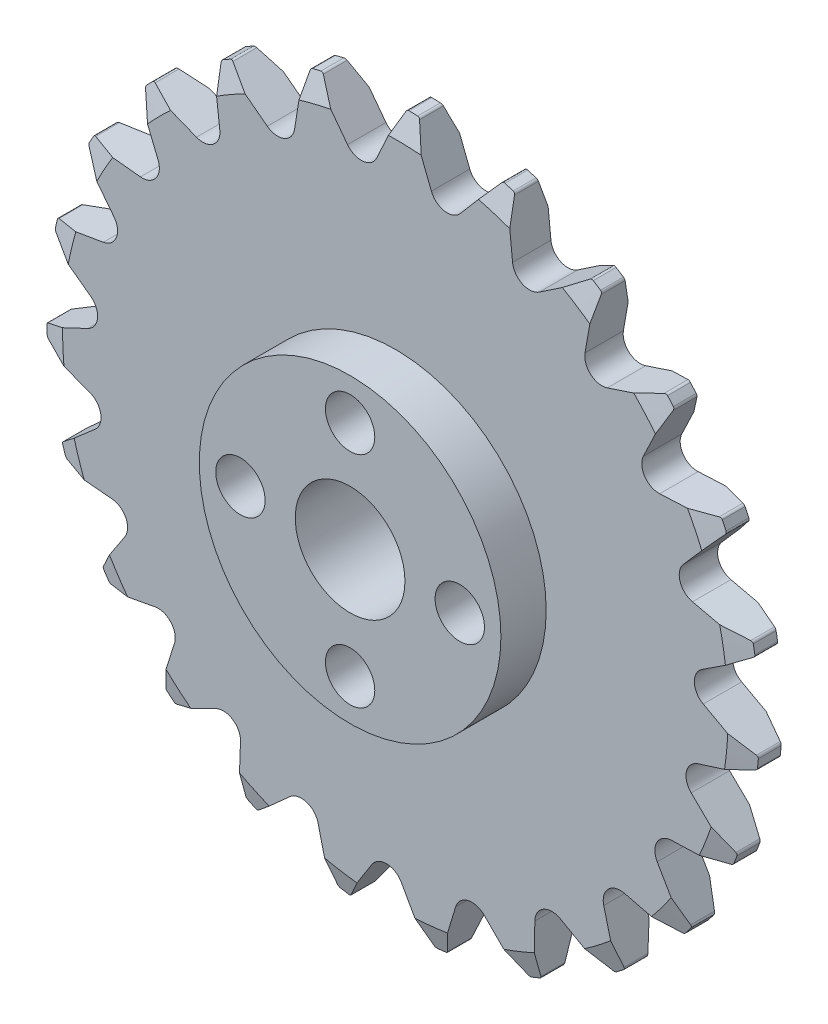
SolidWorks part; units mm, degrees
material "2024 Alloy"
ref_plane "Front Plane" through (0, 0, 0) normal (0, 0, 1) x (1, 0, 0)
ref_plane "Top Plane" through (0, 0, 0) normal (0, 1, 0) x (1, 0, 0)
ref_plane "Right Plane" through (0, 0, 0) normal (1, 0, 0) x (0, 0, -1)
sketch "Sketch1" plane through (0, 0, 0) normal (0, 1, 0) x (1, 0, 0)
  line L0 (26, 2.8) -> (0, 2.8)
  line L1 (0, 2.8) -> (0, 0)
  line L2 (0, 0) -> (26, 0)
  line L3 (26, 0) -> (26, 2.8)
  line L4 (0, 2.8) -> (0, 0) construction
revolve "Revolve1" add sketch "Sketch1" angle 360 about L4
sketch "Sketch2" plane through (0, 0, -2.8) normal (0, 0, -1) x (-1, 0, 0)
  line L0 (18.8013, 17.9586) -> (17.3085, 14.3114)
  line L1 (18.595, 12.5946) -> (22.5146, 13.0035)
  arc A0 (22.5146, 13.0035) -> (18.8013, 17.9586) centre (0, 0) ccw
  arc A1 (17.3085, 14.3114) -> (18.595, 12.5946) centre (18.4653, 13.8379) ccw
extrude "Cut-Extrude1" cut sketch "Sketch2" against normal through all
sketch "Sketch3" plane through (0, 0, -2.8) normal (0, 0, -1) x (-1, 0, 0)
  line L0 (22.9493, 12.2201) -> (20.5278, 9.1109)
  line L1 (21.3035, 7.1107) -> (25.188, 6.4469)
  arc A0 (25.188, 6.4469) -> (22.9493, 12.2201) centre (0, 0) ccw
  arc A1 (20.5278, 9.1109) -> (21.3035, 7.1107) centre (21.514, 8.3429) ccw
extrude "Cut-Extrude2" cut sketch "Sketch3" against normal through all
sketch "Sketch4" plane through (0, 0, -2.8) normal (0, 0, -1) x (-1, 0, 0)
  line L0 (25.3952, 5.5753) -> (22.2247, 3.2347)
  line L1 (22.4319, 1.0994) -> (25.9934, -0.5878)
  arc A0 (25.9934, -0.5878) -> (25.3952, 5.5753) centre (0, 0) ccw
  arc A1 (22.2247, 3.2347) -> (22.4319, 1.0994) centre (22.9671, 2.2291) ccw
extrude "Cut-Extrude3" cut sketch "Sketch4" against normal through all
sketch "Sketch5" plane through (0, 0, -2.8) normal (0, 0, -1) x (-1, 0, 0)
  line L0 (25.9577, -1.483) -> (22.2732, -2.8814)
  line L1 (21.8967, -4.9934) -> (24.8709, -7.5789)
  arc A0 (24.8709, -7.5789) -> (25.9577, -1.483) centre (0, 0) ccw
  arc A1 (22.2732, -2.8814) -> (21.8967, -4.9934) centre (22.7168, -4.05) ccw
extrude "Cut-Extrude4" cut sketch "Sketch5" against normal through all
sketch "Sketch6" plane through (0, 0, -2.8) normal (0, 0, -1) x (-1, 0, 0)
  line L0 (24.595, -8.4313) -> (20.6699, -8.7838)
  line L1 (19.7375, -10.7159) -> (21.9038, -14.0079)
  arc A0 (21.9038, -14.0079) -> (24.595, -8.4313) centre (0, 0) ccw
  arc A1 (20.6699, -8.7838) -> (19.7375, -10.7159) centre (20.7817, -10.0288) ccw
extrude "Cut-Extrude5" cut sketch "Sketch6" against normal through all
sketch "Sketch7" plane through (0, 0, -2.8) normal (0, 0, -1) x (-1, 0, 0)
  line L0 (21.4082, -14.7543) -> (17.5336, -14.0347)
  line L1 (16.1145, -15.6436) -> (17.3123, -19.3981)
  arc A0 (17.3123, -19.3981) -> (21.4082, -14.7543) centre (0, 0) ccw
  arc A1 (17.5336, -14.0347) -> (16.1145, -15.6436) centre (17.3053, -15.2637) ccw
extrude "Cut-Extrude6" cut sketch "Sketch7" against normal through all
sketch "Sketch8" plane through (0, 0, -2.8) normal (0, 0, -1) x (-1, 0, 0)
  line L0 (16.6337, -19.983) -> (13.0969, -18.2448)
  line L1 (11.2963, -19.4112) -> (11.4367, -23.3495)
  arc A0 (11.4367, -23.3495) -> (16.6337, -19.983) centre (0, 0) ccw
  arc A1 (13.0969, -18.2448) -> (11.2963, -19.4112) centre (12.5455, -19.3666) ccw
extrude "Cut-Extrude7" cut sketch "Sketch8" against normal through all
sketch "Sketch9" plane through (0, 0, -2.8) normal (0, 0, -1) x (-1, 0, 0)
  line L0 (10.6255, -23.7297) -> (7.6888, -21.1017)
  line L1 (5.6403, -21.7391) -> (4.713, -25.5693)
  arc A0 (4.713, -25.5693) -> (10.6255, -23.7297) centre (0, 0) ccw
  arc A1 (7.6888, -21.1017) -> (5.6403, -21.7391) centre (6.8552, -22.0332) ccw
extrude "Cut-Extrude8" cut sketch "Sketch9" against normal through all
sketch "Sketch10" plane through (0, 0, -2.8) normal (0, 0, -1) x (-1, 0, 0)
  line L0 (3.8293, -25.7165) -> (1.7105, -22.3936)
  line L1 (-0.4339, -22.4547) -> (-2.3603, -25.8926)
  arc A0 (-2.3603, -25.8926) -> (3.8293, -25.7165) centre (0, 0) ccw
  arc A1 (1.7105, -22.3936) -> (-0.4339, -22.4547) centre (0.6565, -23.0657) ccw
extrude "Cut-Extrude9" cut sketch "Sketch10" against normal through all
sketch "Sketch11" plane through (0, 0, -2.8) normal (0, 0, -1) x (-1, 0, 0)
  line L0 (-3.2509, -25.796) -> (-4.3946, -22.0247)
  line L1 (-6.476, -21.5049) -> (-9.2585, -24.2957)
  arc A0 (-9.2585, -24.2957) -> (-3.2509, -25.796) centre (0, 0) ccw
  arc A1 (-4.3946, -22.0247) -> (-6.476, -21.5049) centre (-5.5908, -22.3875) ccw
extrude "Cut-Extrude10" cut sketch "Sketch11" against normal through all
sketch "Sketch12" plane through (0, 0, -2.8) normal (0, 0, -1) x (-1, 0, 0)
  line L0 (-10.0901, -23.9623) -> (-10.1739, -20.0223)
  line L1 (-12.0379, -18.9602) -> (-15.4701, -20.8968)
  arc A0 (-15.4701, -20.8968) -> (-10.0901, -23.9623) centre (0, 0) ccw
  arc A1 (-10.1739, -20.0223) -> (-12.0379, -18.9602) centre (-11.4236, -20.0489) ccw
extrude "Cut-Extrude11" cut sketch "Sketch12" against normal through all
sketch "Sketch13" plane through (0, 0, -2.8) normal (0, 0, -1) x (-1, 0, 0)
  line L0 (-16.1808, -20.3514) -> (-15.1985, -16.5349)
  line L1 (-16.7069, -15.0093) -> (-20.5343, -15.9481)
  arc A0 (-20.5343, -15.9481) -> (-16.1808, -20.3514) centre (0, 0) ccw
  arc A1 (-15.1985, -16.5349) -> (-16.7069, -15.0093) centre (-16.4091, -16.2234) ccw
extrude "Cut-Extrude12" cut sketch "Sketch13" against normal through all
sketch "Sketch14" plane through (0, 0, -2.8) normal (0, 0, -1) x (-1, 0, 0)
  line L0 (-21.0716, -15.2312) -> (-19.096, -11.8213)
  line L1 (-20.1368, -9.9453) -> (-24.0756, -9.8167)
  arc A0 (-24.0756, -9.8167) -> (-21.0716, -15.2312) centre (0, 0) ccw
  arc A1 (-19.096, -11.8213) -> (-20.1368, -9.9453) centre (-20.1776, -11.1946) ccw
extrude "Cut-Extrude13" cut sketch "Sketch14" against normal through all
sketch "Sketch15" plane through (0, 0, -2.8) normal (0, 0, -1) x (-1, 0, 0)
  line L0 (-24.3995, -8.9813) -> (-21.5772, -6.2309)
  line L1 (-22.0733, -4.1437) -> (-25.8313, -2.9571)
  arc A0 (-25.8313, -2.9571) -> (-24.3995, -8.9813) centre (0, 0) ccw
  arc A1 (-21.5772, -6.2309) -> (-22.0733, -4.1437) centre (-22.4496, -5.3357) ccw
extrude "Cut-Extrude14" cut sketch "Sketch15" against normal through all
sketch "Sketch16" plane through (0, 0, -2.8) normal (0, 0, -1) x (-1, 0, 0)
  line L0 (-25.9178, -2.0654) -> (-22.4581, -0.1783)
  line L1 (-22.3727, 1.9653) -> (-25.6712, 4.1217)
  arc A0 (-25.6712, 4.1217) -> (-25.9178, -2.0654) centre (0, 0) ccw
  arc A1 (-22.4581, -0.1783) -> (-22.3727, 1.9653) centre (-23.0567, 0.919) ccw
extrude "Cut-Extrude15" cut sketch "Sketch16" against normal through all
sketch "Sketch17" plane through (0, 0, -2.8) normal (0, 0, -1) x (-1, 0, 0)
  line L0 (-25.514, 5.0037) -> (-21.6734, 5.8874)
  line L1 (-21.0128, 7.9285) -> (-23.6072, 10.8949)
  arc A0 (-23.6072, 10.8949) -> (-25.514, 5.0037) centre (0, 0) ccw
  arc A1 (-21.6734, 5.8874) -> (-21.0128, 7.9285) centre (-21.9537, 7.1056) ccw
extrude "Cut-Extrude16" cut sketch "Sketch17" against normal through all
sketch "Sketch18" plane through (0, 0, -2.8) normal (0, 0, -1) x (-1, 0, 0)
  line L0 (-23.2178, 11.7018) -> (-19.2813, 11.5165)
  line L1 (-18.0945, 13.3037) -> (-19.7924, 16.86)
  arc A0 (-19.7924, 16.86) -> (-23.2178, 11.7018) centre (0, 0) ccw
  arc A1 (-19.2813, 11.5165) -> (-18.0945, 13.3037) centre (-19.2226, 12.7651) ccw
extrude "Cut-Extrude17" cut sketch "Sketch18" against normal through all
sketch "Sketch19" plane through (0, 0, -2.8) normal (0, 0, -1) x (-1, 0, 0)
  line L0 (-19.1998, 17.5319) -> (-15.4592, 16.2915)
  line L1 (-13.8342, 17.6922) -> (-14.5097, 21.5748)
  arc A0 (-14.5097, 21.5748) -> (-19.1998, 17.5319) centre (0, 0) ccw
  arc A1 (-15.4592, 16.2915) -> (-13.8342, 17.6922) centre (-15.0657, 17.478) ccw
extrude "Cut-Extrude18" cut sketch "Sketch19" against normal through all
sketch "Sketch20" plane through (0, 0, -2.8) normal (0, 0, -1) x (-1, 0, 0)
  line L0 (-13.7577, 22.0618) -> (-10.4905, 19.8582)
  line L1 (-8.5479, 20.7685) -> (-8.1508, 24.6894)
  arc A0 (-8.1508, 24.6894) -> (-13.7577, 22.0618) centre (0, 0) ccw
  arc A1 (-10.4905, 19.8582) -> (-8.5479, 20.7685) centre (-9.7916, 20.8945) ccw
extrude "Cut-Extrude19" cut sketch "Sketch20" against normal through all
sketch "Sketch21" plane through (0, 0, -2.8) normal (0, 0, -1) x (-1, 0, 0)
  line L0 (-7.2953, 24.9555) -> (-4.7438, 21.9521)
  line L1 (-2.6277, 22.3046) -> (-1.1874, 25.9729)
  arc A0 (-1.1874, 25.9729) -> (-7.2953, 24.9555) centre (0, 0) ccw
  arc A1 (-4.7438, 21.9521) -> (-2.6277, 22.3046) centre (-3.7912, 22.7614) ccw
extrude "Cut-Extrude20" cut sketch "Sketch21" against normal through all
sketch "Sketch22" plane through (0, 0, -2.8) normal (0, 0, -1) x (-1, 0, 0)
  line L0 (-0.2919, 25.9984) -> (1.3547, 22.418)
  line L1 (3.4875, 22.1864) -> (5.864, 25.3301)
  arc A0 (5.864, 25.3301) -> (-0.2919, 25.9984) centre (0, 0) ccw
  arc A1 (1.3547, 22.418) -> (3.4875, 22.1864) centre (2.4903, 22.9402) ccw
extrude "Cut-Extrude21" cut sketch "Sketch22" against normal through all
sketch "Sketch23" plane through (0, 0, -2.8) normal (0, 0, -1) x (-1, 0, 0)
  line L0 (6.7332, 25.113) -> (7.3527, 21.2211)
  line L1 (9.344, 20.4228) -> (12.4805, 22.8087)
  arc A0 (12.4805, 22.8087) -> (6.7332, 25.113) centre (0, 0) ccw
  arc A1 (7.3527, 21.2211) -> (9.344, 20.4228) centre (8.5872, 21.4176) ccw
extrude "Cut-Extrude22" cut sketch "Sketch23" against normal through all
sketch "Sketch24" plane through (0, 0, -2.8) normal (0, 0, -1) x (-1, 0, 0)
  line L0 (13.2589, 22.3652) -> (12.8055, 18.4505)
  line L1 (14.5075, 17.1445) -> (18.1714, 18.5957)
  arc A0 (18.1714, 18.5957) -> (13.2589, 22.3652) centre (0, 0) ccw
  arc A1 (12.8055, 18.4505) -> (14.5075, 17.1445) centre (14.0472, 18.3066) ccw
extrude "Cut-Extrude23" cut sketch "Sketch24" against normal through all
sketch "Sketch25" plane through (0, 0, 0) normal (0, 1, 0) x (1, 0, 0)
  line L0 (11, 0) -> (0, 0)
  line L1 (0, 0) -> (0, -3.302)
  line L2 (0, -3.302) -> (11, -3.302)
  line L3 (11, -3.302) -> (11, 0)
  line L4 (0, 0) -> (0, -3.302) construction
revolve "Revolve2" add sketch "Sketch25" angle 360 about L4
hole_wizard "Ø8.0 (8) Diameter Hole1" positions "Sketch27" profile "Sketch26" hole size "Ø8.0" standard "ANSI Metric"
sketch "Sketch27" plane through (0, 0, 3.302) normal (0, 0, 1) x (1, 0, 0)
  point P0 (0, 0)
sketch "Sketch26" plane through (0, 0, 3.302) normal (1, 0, 0) x (0, -1, 0)
  line L0 (0, 0) -> (0, 6.102)
  line L1 (0, 6.102) -> (4, 6.102)
  line L2 (4, 6.102) -> (4, 0)
  line L5 (4, 0) -> (0, 0)
  line L11 (0, -6.35) -> (0, 107.95) construction
  dimension "Thru Hole Dia." = 8
  dimension "Thru Hole Depth" = 6.102
hole_wizard "Ø3.6 (3.6) Diameter Hole1" positions "Sketch29" profile "Sketch28" hole size "Ø3.6" standard "ANSI Metric"
sketch "Sketch29" plane through (0, 0, 3.302) normal (0, 0, 1) x (1, 0, 0)
  point P0 (0, 8)
  point P1 (-8, 0)
  point P2 (0, -8)
sketch "Sketch28" plane through (0, 8, 3.302) normal (1, 0, 0) x (0, -1, 0)
  line L0 (0, 0) -> (0, 6.102)
  line L1 (0, 6.102) -> (1.8, 6.102)
  line L2 (1.8, 6.102) -> (1.8, 0)
  line L5 (1.8, 0) -> (0, 0)
  line L11 (0, -6.35) -> (0, 107.95) construction
  dimension "Thru Hole Dia." = 3.6
  dimension "Thru Hole Depth" = 6.102
hole_wizard "Ø3.6 (3.6) Diameter Hole2" positions "Sketch31" profile "Sketch30" hole size "Ø3.6" standard "ANSI Metric"
sketch "Sketch31" plane through (0, 0, -2.8) normal (0, 0, -1) x (-1, 0, 0)
  point P0 (-8, 0)
sketch "Sketch30" plane through (8, 0, -2.8) normal (1, 0, 0) x (0, 1, 0)
  line L0 (0, 0) -> (0, 6.102)
  line L1 (0, 6.102) -> (1.8, 6.102)
  line L2 (1.8, 6.102) -> (1.8, 0)
  line L5 (1.8, 0) -> (0, 0)
  line L11 (0, -6.35) -> (0, 107.95) construction
  dimension "Thru Hole Dia." = 3.6
  dimension "Thru Hole Depth" = 6.102
fillet "Fillet1" radius 0.2 46 edges at (25.8313, -2.9571, -1.4) (25.9178, -2.0654, -1.4) (9.2585, -24.2957, -1.4) (10.0901, -23.9623, -1.4) (14.5097, 21.5748, -1.4) (13.7577, 22.0618, -1.4) (-13.2589, 22.3652, -1.4) (-12.4805, 22.8087, -1.4) (20.5343, -15.9481, -1.4) (21.0716, -15.2312, -1.4) (-18.8013, 17.9586, -1.4) (-18.1714, 18.5957, -1.4) (23.6072, 10.8949, -1.4) (23.2178, 11.7018, -1.4) (1.1874, 25.9729, -1.4) (0.2919, 25.9984, -1.4) (-22.9493, 12.2201, -1.4) (-22.5146, 13.0035, -1.4) (15.4701, -20.8968, -1.4) (16.1808, -20.3514, -1.4) (24.0756, -9.8167, -1.4) (24.3995, -8.9813, -1.4) (-25.3952, 5.5753, -1.4) (-25.188, 6.4469, -1.4) (25.6712, 4.1217, -1.4) (25.514, 5.0037, -1.4) (19.7924, 16.86, -1.4) (19.1998, 17.5319, -1.4) (-25.9577, -1.483, -1.4) (-25.9934, -0.5878, -1.4) (8.1508, 24.6894, -1.4) (7.2953, 24.9555, -1.4) (-5.864, 25.3301, -1.4) (-6.7332, 25.113, -1.4) (-24.595, -8.4313, -1.4) (-24.8709, -7.5789, -1.4) (-21.4082, -14.7543, -1.4) (-21.9038, -14.0079, -1.4) (-16.6337, -19.983, -1.4) (-17.3123, -19.3981, -1.4) (-10.6255, -23.7297, -1.4) (-11.4367, -23.3495, -1.4) (-3.8293, -25.7165, -1.4) (-4.713, -25.5693, -1.4) (3.2509, -25.796, -1.4) (2.3603, -25.8926, -1.4)
sketch "Sketch32" plane through (0, 0, 0) normal (1, 0, 0) x (0, 0, -1)
  line L0 (0, 24.2697) -> (0, 26.0477)
  line L1 (0, 26.0477) -> (0.5842, 26.0477)
  line L2 (0.5842, 26.0477) -> (0, 24.2697)
  line L3 (1.4, 25.8518) -> (1.4, 8.3868) construction
  line L4 (2.8, 25.8518) -> (0, 25.8518) construction
  line L5 (0, 0) -> (13.057, 0) construction
  line L6 (2.2158, 26.0477) -> (2.8, 24.2697)
  line L7 (2.8, 26.0477) -> (2.2158, 26.0477)
  line L8 (2.8, 24.2697) -> (2.8, 26.0477)
  dimension "D1" = 24.2697
  dimension "D2" = 1.778
  dimension "D3" = 0.5842
revolve "Cut-Revolve1" cut sketch "Sketch32" angle 360 about L5
